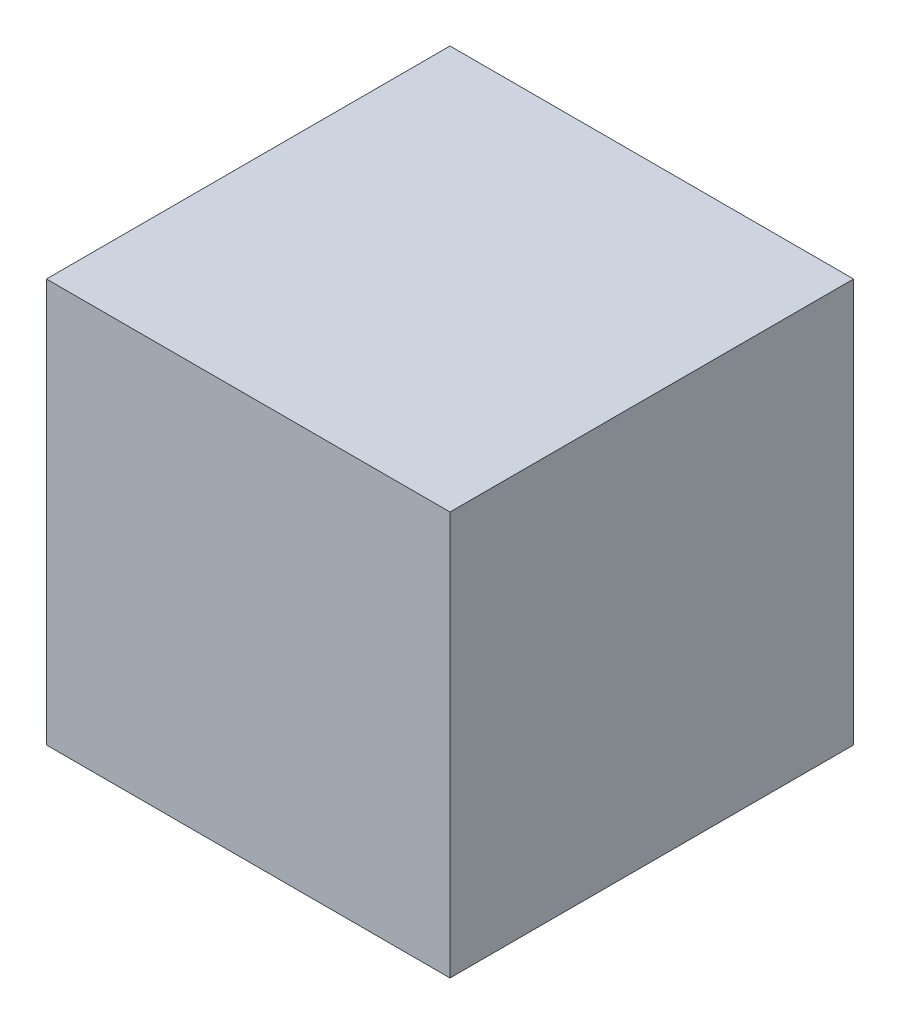
SolidWorks part; units mm, degrees
ref_plane "Front Plane" through (0, 0, 0) normal (0, 0, 1) x (1, 0, 0)
ref_plane "Top Plane" through (0, 0, 0) normal (0, 1, 0) x (1, 0, 0)
ref_plane "Right Plane" through (0, 0, 0) normal (1, 0, 0) x (0, 0, -1)
sketch "Sketch1" plane through (0, 0, 0) normal (0, 0, 1) x (1, 0, 0)
  line L1 (-152.4, -152.4) -> (152.4, -152.4)
  line L2 (-152.4, -152.4) -> (-152.4, 152.4)
  line L3 (-152.4, 152.4) -> (152.4, 152.4)
  line L4 (152.4, -152.4) -> (152.4, 152.4)
  line L5 (-152.4, -152.4) -> (152.4, 152.4) construction
  line L6 (-152.4, 152.4) -> (152.4, -152.4) construction
  point P0 (0, 0)
  dimension "D1" = 304.8
  dimension "D2" = 304.8
extrude "Boss-Extrude1" add sketch "Sketch1" against normal blind 304.8
